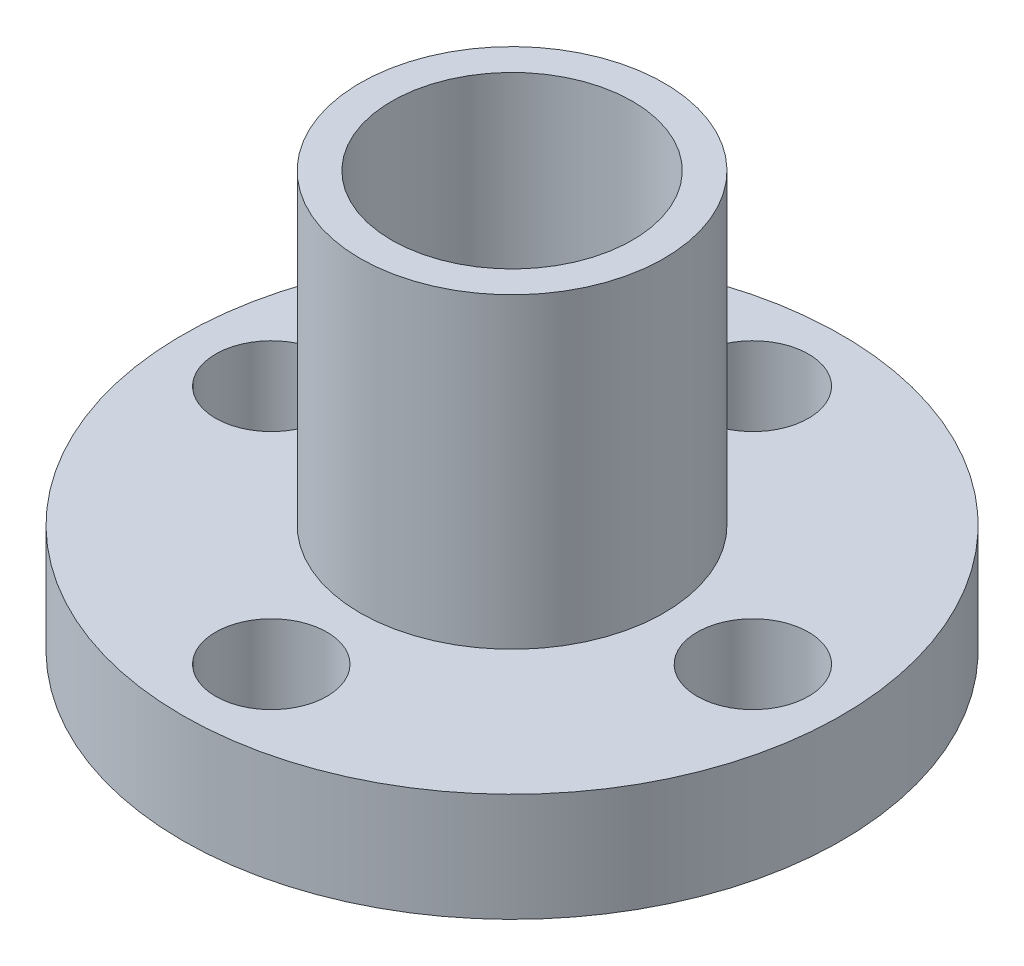
SolidWorks part; units mm, degrees
ref_plane "Front Plane" through (0, 0, 0) normal (0, 0, 1) x (1, 0, 0)
ref_plane "Top Plane" through (0, 0, 0) normal (0, 1, 0) x (1, 0, 0)
ref_plane "Right Plane" through (0, 0, 0) normal (1, 0, 0) x (0, 0, -1)
sketch "Sketch1" plane through (0, 0, 0) normal (0, 1, 0) x (1, 0, 0)
  circle A0 centre (0, 0) radius 10.95
  dimension "D1" = 21.9
extrude "Boss-Extrude1" add sketch "Sketch1" along normal blind 3.6
sketch "Sketch2" plane through (0, 3.6, 0) normal (0, 1, 0) x (1, 0, 0)
  circle A0 centre (0, 0) radius 5.05
  circle A1 centre (0, 0) radius 4
  dimension "D1" = 10.1
  dimension "D2" = 8
extrude "Boss-Extrude2" add sketch "Sketch2" along normal blind 10.2
sketch "Sketch3" plane through (0, 0, 0) normal (0, -1, 0) x (1, 0, 0)
  circle A0 centre (0, 0) radius 4 construction
  circle A1 centre (0, 0) radius 5.05
  circle A2 centre (0, 0) radius 5.05
  circle A3 centre (0, 0) radius 4
  dimension "D1" = 0
extrude "Boss-Extrude4" add sketch "Sketch3" along normal blind 0.65
sketch "Sketch4" plane through (0, 3.6, 0) normal (0, 1, 0) x (1, 0, 0)
  circle A0 centre (0, 8) radius 1.85
  circle A1 centre (0, 0) radius 4
  circle A2 centre (0, 0) radius 4
  circle A5 centre (8, 0) radius 1.85
  circle A6 centre (0, -8) radius 1.85
  circle A7 centre (-8, 0) radius 1.85
  point P15 (0, 0)
  point P21 (0, 0)
  dimension "D2" = 3.7
  dimension "D3" = 8
  dimension "D1" = 0
extrude "Cut-Extrude1" cut sketch "Sketch4" against normal through all both and the other way through all
